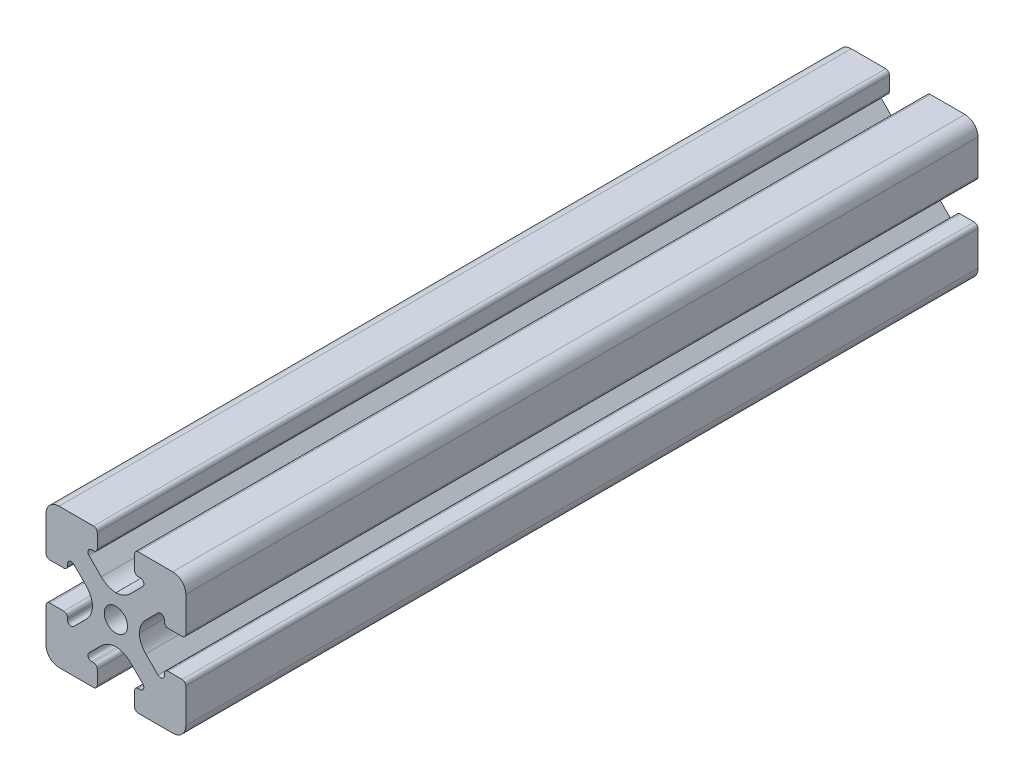
SolidWorks part; units mm, degrees
ref_plane "Front Plane" through (0, 0, 0) normal (0, 0, 1) x (1, 0, 0)
ref_plane "Top Plane" through (0, 0, 0) normal (0, 1, 0) x (1, 0, 0)
ref_plane "Right Plane" through (0, 0, 0) normal (1, 0, 0) x (0, 0, -1)
sketch "Sketch2" plane through (0, 0, 0) normal (0, 0, 1) x (1, 0, 0)
  line L0 (0, 7.5) -> (0, -7.5) construction
  line L1 (-7.5, 0) -> (7.5, 0) construction
  line L2 (2, -7.5) -> (7.5, -7.5)
  line L3 (7.5, -7.5) -> (7.5, -2)
  line L4 (2, -7.5) -> (2, -5.1953)
  line L5 (2, -5.1953) -> (3.5657, -5.1953)
  line L6 (3.5657, -5.1953) -> (0.8704, -2.5)
  line L7 (0, 0) -> (7.5, -7.5) construction
  line L8 (7.5, -2) -> (5.1953, -2)
  line L9 (5.1953, -2) -> (5.1953, -3.5657)
  line L10 (5.1953, -3.5657) -> (2.5, -0.8704)
  line L11 (3.8477, -2.218) -> (2.218, -3.8477) construction
  circle A0 centre (0, 0) radius 1.25
  arc A1 (2.6, -5.1953) -> (2.8828, -4.5125) centre (2.6, -4.7953) ccw construction
  point P8 (0, -2.5)
  point P16 (3.0328, -3.0328)
  dimension "Center Hole Diameter" = 2.5
  dimension "D3" = 0.4
  dimension "Rail Height" = 15
  dimension "Rail Width" = 15
  dimension "T-Slot Width" = 4
  dimension "Slot Depth" = 5
  dimension "Slot Inner Width" = 6
sketch "Sketch3" plane through (0, 0, 0) normal (1, 0, 0) x (0, 0, -1)
  line L0 (-42.5, -7.5) -> (42.5, -7.5) construction
  line L1 (-17.1, 0) -> (17.1, 0) construction
  line L2 (0, 7.5) -> (0, -7.5) construction
  line L3 (0, 7.5) -> (0, -7.5) construction
  point P6 (-17.1, 0)
  point P8 (17.1, 0)
  dimension "Length" = 85
  dimension "D1" = 25.4
sketch "Sketch4" plane through (0, 0, 0) normal (0, 0, 1) x (1, 0, 0)
  line L0 (2.4, -7.5) -> (6.1, -7.5)
  line L1 (2, -7.5) -> (7.5, -7.5) construction
  line L2 (2, -7.5) -> (2, -5.1953) construction
  line L3 (2, -5.1953) -> (3.5657, -5.1953) construction
  line L4 (2, -5.5953) -> (2, -7.1)
  line L5 (2.4, -5.1953) -> (2.6, -5.1953)
  line L6 (0, -2.5) -> (-0.1238, -2.5)
  line L7 (3.5657, -5.1953) -> (0.8704, -2.5) construction
  line L8 (1.5733, -3.2029) -> (2.8828, -4.5125)
  line L9 (7.5, -7.5) -> (7.5, -2) construction
  line L10 (5.1953, -3.5657) -> (2.5, -0.8704) construction
  line L11 (5.1953, -2) -> (5.1953, -3.5657) construction
  line L12 (5.1953, -2.6) -> (5.1953, -2.4)
  line L13 (7.5, -2) -> (5.1953, -2) construction
  line L14 (5.5953, -2) -> (7.1, -2)
  line L15 (7.5, -2.4) -> (7.5, -6.1)
  line L16 (4.5125, -2.8828) -> (3.2029, -1.5733)
  line L17 (2.5, 0) -> (2.5, 0.1238)
  line L18 (-7.5, 0) -> (7.5, 0) construction
  line L19 (0, -2.5) -> (0, -1.25)
  line L20 (0, 7.5) -> (0, -7.5) construction
  line L21 (2.5, 0) -> (1.25, 0)
  arc A0 (2, -7.1) -> (2.4, -7.5) centre (2.4, -7.1) ccw
  arc A1 (2.6, -5.1953) -> (2.8828, -4.5125) centre (2.6, -4.7953) ccw construction
  arc A2 (2, -5.5953) -> (2.4, -5.1953) centre (2.4, -5.5953) cw
  arc A3 (2.6, -5.1953) -> (2.8828, -4.5125) centre (2.6, -4.7953) ccw
  arc A4 (-0.1238, -2.5) -> (1.5733, -3.2029) centre (-0.1238, -4.9) cw
  arc A5 (6.1, -7.5) -> (7.5, -6.1) centre (6.1, -6.1) ccw
  arc A6 (4.5125, -2.8828) -> (5.1953, -2.6) centre (4.7953, -2.6) ccw
  arc A7 (5.1953, -2.4) -> (5.5953, -2) centre (5.5953, -2.4) cw
  arc A8 (7.1, -2) -> (7.5, -2.4) centre (7.1, -2.4) cw
  arc A9 (3.2029, -1.5733) -> (2.5, 0.1238) centre (4.9, 0.1238) cw
  circle A10 centre (0, 0) radius 1.25 construction
  arc A11 (0, -1.25) -> (1.25, 0) centre (0, 0) ccw
  dimension "D1" = 1.4
  dimension "D2" = 2.4
extrude "Boss-Extrude1" add sketch "Sketch4" along normal mid plane 85
mirror "Mirror1" about plane through (0, 0, 0) normal (1, 0, 0) of bodies 134
mirror "Mirror2" about plane through (0, 0, 0) normal (0, 1, 0) of bodies 135
equation "\"D3@Sketch2\"=\"T-Slot Width@Sketch2\"*0.1"
equation "\"D1@Sketch4\"=\"D3@Sketch2\"*3.5"
equation "\"D2@Sketch4\"=\"D3@Sketch2\"*6"
equation "\"D1@Boss-Extrude1\"=\"Length@Sketch3\""
